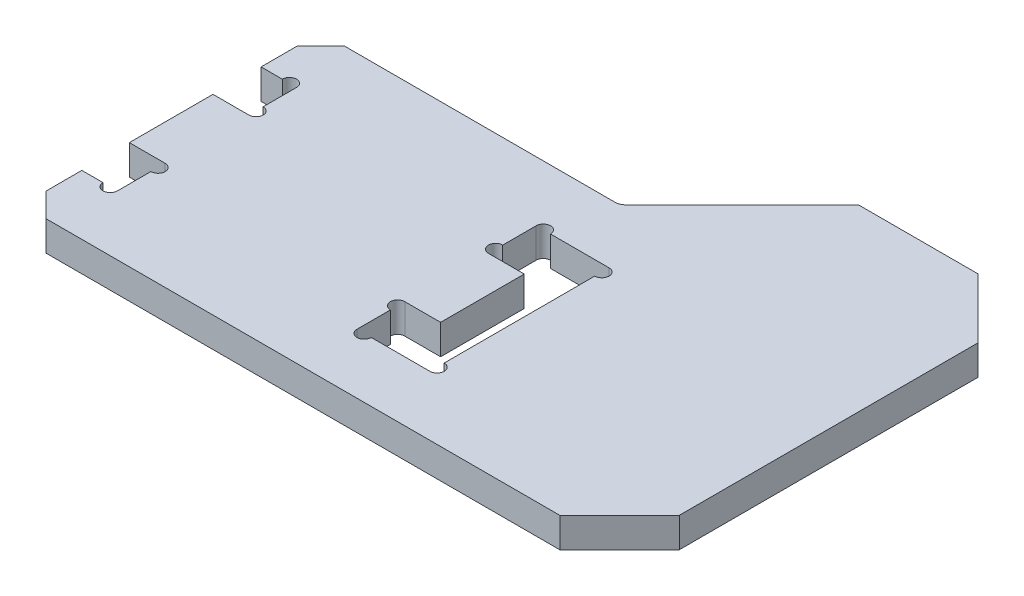
SolidWorks part; units mm, degrees
ref_plane "前视基准面" through (0, 0, 0) normal (0, 0, 1) x (1, 0, 0)
ref_plane "上视基准面" through (0, 0, 0) normal (0, 1, 0) x (1, 0, 0)
ref_plane "右视基准面" through (0, 0, 0) normal (1, 0, 0) x (0, 0, -1)
sketch "草图1" plane through (0, 0, 0) normal (0, 1, 0) x (1, 0, 0)
  line L0 (-25, 12.5) -> (0, 12.5)
  line L1 (0, 12.5) -> (10, 22.5)
  line L2 (10, 22.5) -> (25, 22.5)
  line L3 (25, 22.5) -> (25, -12.5)
  line L4 (25, -12.5) -> (-25, -12.5)
  line L5 (-25, -12.5) -> (-25, -7.5)
  line L6 (-25, 7.5) -> (-22.025, 7.5)
  line L7 (-22.025, 7.5) -> (-22.025, 3.5)
  line L8 (-22.025, 3.5) -> (-25.025, 3.5)
  line L9 (-25.025, -3.5) -> (-22.025, -3.5)
  line L10 (-22.025, -3.5) -> (-22.025, -7.5)
  line L11 (-22.025, -7.5) -> (-25, -7.5)
  line L12 (-25, 7.5) -> (-25, 12.5)
  line L13 (-25.025, -3.5) -> (-25.025, 3.5)
  line L14 (-12, 12.5) -> (-12, -12.5) construction
  line L15 (-1.975, -3.5) -> (-1.975, -7.5)
  line L16 (1.025, -3.5) -> (-1.975, -3.5)
  line L17 (1.025, -3.5) -> (1.025, 3.5)
  line L18 (-1.975, 3.5) -> (1.025, 3.5)
  line L19 (-1.975, 7.5) -> (-1.975, 3.5)
  line L20 (-1.975, 7.5) -> (4.125, 7.5)
  line L21 (4.125, 7.5) -> (4.125, -7.5)
  line L22 (4.125, -7.5) -> (-1.975, -7.5)
  point P7 (-25.025, 0)
  point P8 (0, -12.5)
  dimension "D1" = 50
  dimension "D2" = 7
  dimension "D3" = 15
  dimension "D4" = 3.1
  dimension "D5" = 3
  dimension "D6" = 20.05
  dimension "D7" = 13
  dimension "D8" = 45
  dimension "D9" = 25
  dimension "D10" = 15
  dimension "D11" = 35
extrude "凸台-拉伸1" add sketch "草图1" along normal mid plane 2.5
sketch "草图2" plane through (0, 1.25, 0) normal (0, 1, 0) x (1, 0, 0)
  line L0 (-22.025, 7.5) -> (-22.025, 3.5) construction
  line L1 (-25, 7.5) -> (-22.025, 7.5) construction
  line L2 (-22.025, -7.5) -> (-25, -7.5) construction
  line L3 (-22.025, -3.5) -> (-22.025, -7.5) construction
  line L4 (-1.975, 7.5) -> (-1.975, 3.5) construction
  line L5 (4.125, 7.5) -> (-1.975, 7.5) construction
  line L6 (-1.975, -7.5) -> (4.125, -7.5) construction
  line L7 (-1.975, -3.5) -> (-1.975, -7.5) construction
  line L8 (4.125, -7.5) -> (4.125, 7.5) construction
  circle A0 centre (-22.025, 4.1) radius 0.6
  circle A1 centre (-22.625, 7.5) radius 0.6
  circle A2 centre (-22.625, -7.5) radius 0.6
  circle A3 centre (-22.025, -4.1) radius 0.6
  circle A4 centre (-1.975, 4.1) radius 0.6
  circle A5 centre (-1.375, 7.5) radius 0.6
  circle A6 centre (-1.375, -7.5) radius 0.6
  circle A7 centre (-1.975, -4.1) radius 0.6
  circle A8 centre (4.125, -6.9) radius 0.6
  circle A9 centre (4.125, 6.9) radius 0.6
  dimension "D1" = 1.2
extrude "切除-拉伸1" cut sketch "草图2" against normal through all
chamfer "倒角2" distance 2 angle 45 2 edges at (-25, 0, 12.5) (-25, 0, -12.5)
fillet "圆角1" radius 1 1 edges at (0, 0, -12.5)
chamfer "倒角3" distance 5 angle 45 2 edges at (25, 0, -22.5) (25, 0, 12.5)
